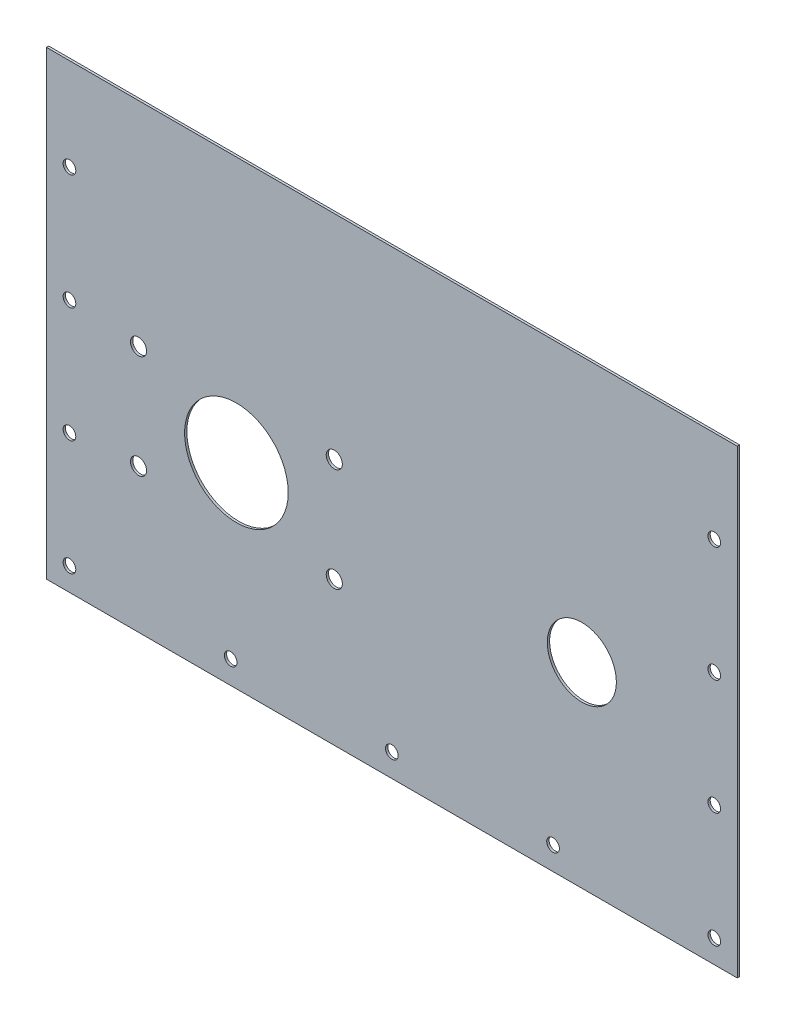
SolidWorks part; units mm, degrees
ref_plane "정면" through (0, 0, 0) normal (0, 0, 1) x (1, 0, 0)
ref_plane "윗면" through (0, 0, 0) normal (0, 1, 0) x (1, 0, 0)
ref_plane "우측면" through (0, 0, 0) normal (1, 0, 0) x (0, 0, -1)
sketch "스케치1" plane through (0, 0, 0) normal (0, 0, 1) x (1, 0, 0)
  line L1 (-150, -110) -> (150, -110)
  line L2 (-150, -110) -> (-150, 110)
  line L3 (-150, 110) -> (150, 110)
  line L4 (150, -110) -> (150, 110)
  line L5 (-150, -110) -> (150, 110) construction
  line L6 (-150, 110) -> (150, -110) construction
  line L7 (-140, -100) -> (140, -100) construction
  line L8 (-140, -100) -> (-140, 100) construction
  line L9 (-140, 100) -> (140, 100) construction
  line L10 (140, -100) -> (140, 100) construction
  line L11 (-140, -100) -> (140, 100) construction
  line L12 (-140, 100) -> (140, -100) construction
  point P0 (0, 0)
  point P6 (0, 0)
  point P12 (-140, 100)
  point P13 (140, 100)
  point P14 (140, -100)
  point P15 (-140, -100)
  point P16 (0, -100)
  point P17 (-70, -100)
  point P19 (70, -100)
  point P20 (-140, -50)
  point P22 (0, 100)
  point P23 (-70, 100)
  point P25 (70, 100)
  point P26 (-140, 0)
  point P27 (0, 100)
  point P29 (-140, 50)
  point P32 (140, -50)
  point P33 (140, 0)
  point P35 (140, 50)
  dimension "D1" = 300
  dimension "D2" = 220
  dimension "D3" = 10
  dimension "D4" = 10
  dimension "D5" = 50
  dimension "D6" = 50
  dimension "D7" = 70
  dimension "D8" = 70
extrude "보스-돌출1" add sketch "스케치1" along normal blind 1 contours L3 L4 L1 L2
hole_wizard "M5 여유 구멍1" positions "스케치2" profile "스케치3" hole size "M5" standard "KS" end condition through all
sketch "스케치2" plane through (0, 0, 0) normal (0, 0, -1) x (-1, 0, 0)
  point P0 (-140, 100)
  point P3 (-70, 100)
  point P6 (70, 100)
  point P9 (0, 100)
  point P18 (140, 100)
  point P21 (140, 50)
  point P24 (140, -50)
  point P27 (140, 0)
  point P36 (140, -100)
  point P39 (-140, 50)
  point P42 (-140, -50)
  point P45 (-140, 0)
  point P54 (-140, -100)
  point P57 (-70, -100)
  point P60 (70, -100)
  point P63 (0, -100)
sketch "스케치3" plane through (140, 100, 0) normal (1, 0, 0) x (0, 1, 0)
  line L0 (0, 0) -> (0, 1)
  line L1 (0, 1) -> (2.75, 1)
  line L2 (2.75, 1) -> (2.75, 0)
  line L5 (2.75, 0) -> (0, 0)
  line L11 (0, -6.35) -> (0, 107.95) construction
  dimension "관통 구멍 지름" = 5.5
  dimension "관통 구멍 깊이" = 1
sketch "스케치4" plane through (0, 0, 1) normal (0, 0, 1) x (1, 0, 0)
  line L0 (150, -110) -> (150, 110) construction
  line L1 (-150, 110) -> (150, 110)
  line L2 (-150, 110) -> (-150, 90)
  line L3 (-150, 90) -> (150, 90)
  line L4 (150, 110) -> (150, 90)
  line L5 (-150, 110) -> (150, 90) construction
  line L6 (-150, 90) -> (150, 110) construction
  point P4 (0, 100)
  dimension "D1" = 20
extrude "컷-돌출1" cut sketch "스케치4" against normal blind 10 contours L3 L4 L1 L2
sketch "스케치5" plane through (0, 0, 1) normal (0, 0, 1) x (1, 0, 0)
  line L0 (15, -25) -> (-150, -25) construction
  line L1 (-150, -110) -> (-150, 90) construction
  line L2 (15, -25) -> (150, -25) construction
  line L3 (150, -110) -> (150, 90) construction
  line L5 (-115, 2.5) -> (-20, 2.5)
  line L6 (-115, 2.5) -> (-115, -52.5)
  line L7 (-115, -52.5) -> (-20, -52.5)
  line L8 (-20, 2.5) -> (-20, -52.5)
  line L9 (-115, 2.5) -> (-20, -52.5) construction
  line L10 (-115, -52.5) -> (-20, 2.5) construction
  circle A0 centre (-67.5, -25) radius 22.5
  circle A1 centre (82.5, -25) radius 15
  circle A2 centre (-25, -47.5) radius 3.5
  circle A5 centre (-25, -2.5) radius 3.5
  circle A6 centre (-110, -47.5) radius 3.5
  circle A7 centre (-110, -2.5) radius 3.5
  point P10 (82.5, -25)
  point P15 (-67.5, -25)
  point P18 (-67.5, -25)
  dimension "D1" = 45
  dimension "D3" = 30
  dimension "D9" = 7
  dimension "D2" = 95
  dimension "D4" = 55
  dimension "D5" = 5
  dimension "D6" = 5
  dimension "D7" = 5
  dimension "D8" = 5
  dimension "D10" = 5
  dimension "D11" = 25
  dimension "D12" = 15
extrude "컷-돌출2" cut sketch "스케치5" against normal blind 10 contours A0 | A1 | A7 | A6 | A2 | A5
